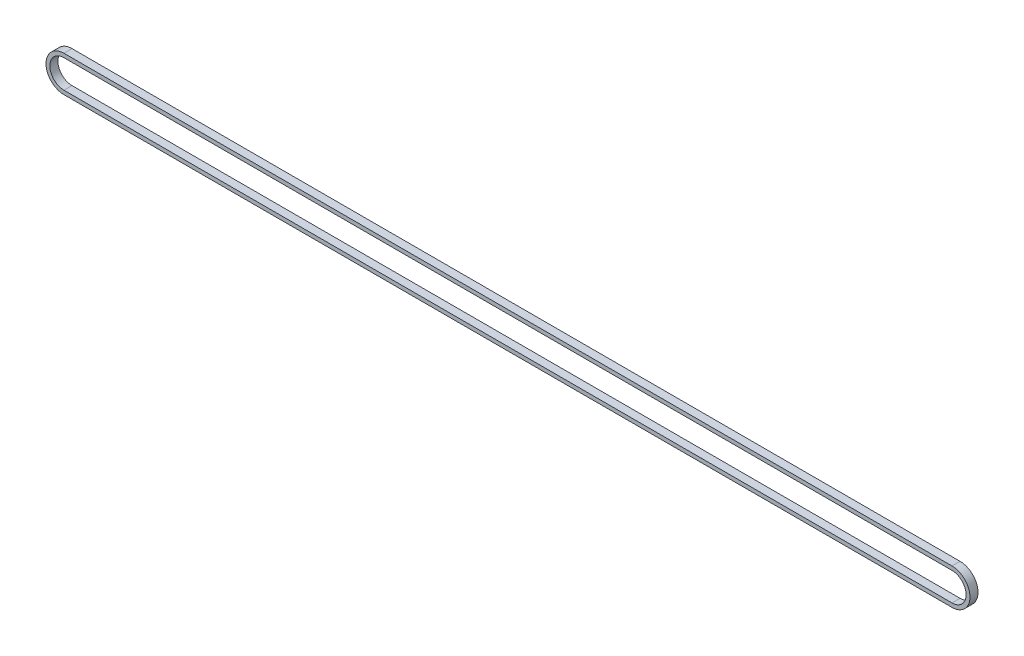
SolidWorks part; units mm, degrees
material "Rubber"
ref_plane "Front Plane" through (0, 0, 0) normal (0, 0, 1) x (1, 0, 0)
ref_plane "Top Plane" through (0, 0, 0) normal (0, 1, 0) x (1, 0, 0)
ref_plane "Right Plane" through (0, 0, 0) normal (1, 0, 0) x (0, 0, -1)
sketch "Sketch1" plane through (0, 0, 0) normal (0, 0, 1) x (1, 0, 0)
  line L0 (0, 0) -> (551.8, 0) construction
  line L1 (0, 8.75) -> (551.8, 8.75)
  line L2 (551.8, -8.75) -> (0, -8.75)
  arc A0 (0, 8.75) -> (0, -8.75) centre (0, 0) ccw
  arc A1 (551.8, -8.75) -> (551.8, 8.75) centre (551.8, 0) ccw
  dimension "D1" = 17.5
  dimension "D2" = 551.8
extrude "Extrude-Thin1" add sketch "Sketch1" along normal mid plane 5 thin thin type one direction wall 2.4
